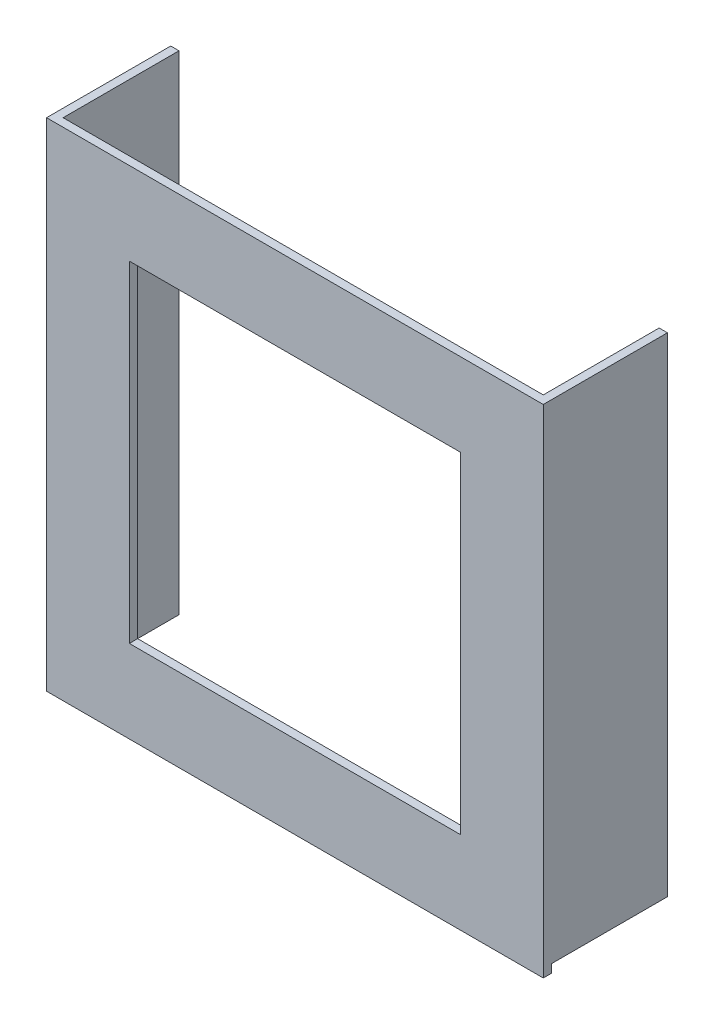
SolidWorks part; units mm, degrees
material "ABS"
ref_plane "Front Plane" through (0, 0, 0) normal (0, 0, 1) x (1, 0, 0)
ref_plane "Top Plane" through (0, 0, 0) normal (0, 1, 0) x (1, 0, 0)
ref_plane "Right Plane" through (0, 0, 0) normal (1, 0, 0) x (0, 0, -1)
sketch "Sketch1" plane through (0, 0, 0) normal (0, 0, 1) x (1, 0, 0)
  line L1 (-150, 150) -> (150, 150)
  line L2 (-150, 150) -> (-150, -150)
  line L3 (-150, -150) -> (150, -150)
  line L4 (150, 150) -> (150, -150)
  line L5 (-150, 150) -> (150, -150) construction
  line L6 (-150, -150) -> (150, 150) construction
  line L7 (-100, 100) -> (100, 100)
  line L8 (-100, 100) -> (-100, -100)
  line L9 (-100, -100) -> (100, -100)
  line L10 (100, 100) -> (100, -100)
  line L11 (-100, 100) -> (100, -100) construction
  line L12 (-100, -100) -> (100, 100) construction
  point P0 (0, 0)
  point P6 (0, 0)
  dimension "D1" = 300
  dimension "D2" = 200
extrude "Boss-Extrude1" add sketch "Sketch1" along normal blind 5
sketch "Sketch2" plane through (0, 0, 0) normal (0, 0, -1) x (-1, 0, 0)
  line L0 (-145, -145) -> (-150, -145)
  line L1 (-150, 150) -> (150, 150)
  line L2 (-150, 150) -> (-150, -150)
  line L3 (-150, -150) -> (150, -150)
  line L4 (150, 150) -> (150, -150)
  line L5 (-150, 150) -> (150, -150) construction
  line L6 (-150, -150) -> (150, 150) construction
  line L7 (-145, 145) -> (145, 145)
  line L8 (-145, 145) -> (-145, -145)
  line L9 (-145, -145) -> (145, -145)
  line L10 (145, 145) -> (145, -145)
  line L11 (-145, 145) -> (145, -145) construction
  line L12 (-145, -145) -> (145, 145) construction
  line L13 (145, -145) -> (150, -145)
  line L14 (-145, 145) -> (-145, 150)
  line L15 (145, 145) -> (145, 150)
  point P0 (0, 0)
  point P7 (0, 0)
  point P16 (-145, -145)
  line M6 (-150, 150) -> (-150, -150)
  line M9 (150, 150) -> (-150, 150)
  dimension "D1" = 5
extrude "Boss-Extrude5" add sketch "Sketch2" along normal blind 70 contours L8 L14 L1 L0 M6 | L15 L10 L13 L4 M9
